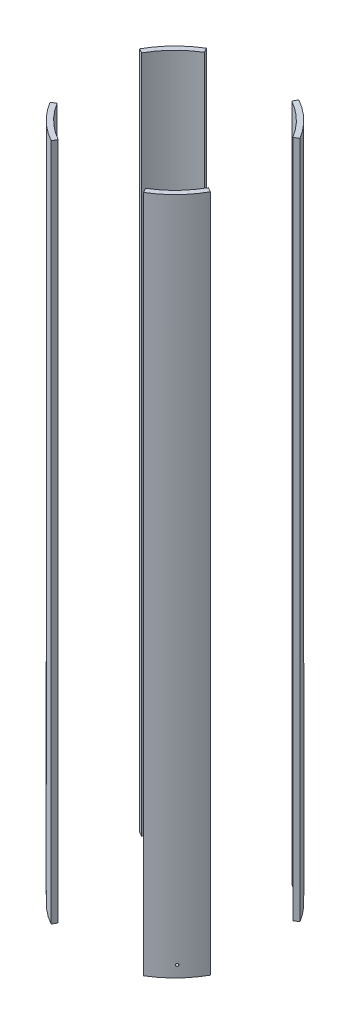
SolidWorks part; units mm, degrees
material "6061-T6 (SS)"
ref_plane "Front Plane" through (0, 0, 0) normal (0, 0, 1) x (1, 0, 0)
ref_plane "Top Plane" through (0, 0, 0) normal (0, 1, 0) x (1, 0, 0)
ref_plane "Right Plane" through (0, 0, 0) normal (1, 0, 0) x (0, 0, -1)
sketch "Sketch2" plane through (0, 0, 0) normal (0, 1, 0) x (1, 0, 0)
  circle A0 centre (0, 0) radius 88.9
  circle A1 centre (0, 0) radius 83.82
  dimension "D1" = 177.8
  dimension "D2" = 167.64
extrude "Boss-Extrude1" add sketch "Sketch2" along normal mid plane 662.3682
sketch "Sketch3" plane through (0, 0, 0) normal (0, 1, 0) x (1, 0, 0)
  line L0 (0, 0) -> (169.6618, 101.6776)
  line L1 (-58.1167, 96.9749) -> (0, 0)
  line L2 (0, 0) -> (53.9, 96.9749)
  line L3 (53.9, 96.9749) -> (-58.1167, 96.9749)
  line L4 (0, 0) -> (70.9917, -118.4586)
  line L5 (70.9917, -118.4586) -> (-65.8409, -118.4586)
  line L6 (-65.8409, -118.4586) -> (0, 0)
  line L7 (169.6618, 101.6776) -> (169.6618, -94.3004)
  line L8 (169.6618, -94.3004) -> (0, 0)
  line L9 (0, 0) -> (-123.7413, 68.7771)
  line L10 (-123.7413, 68.7771) -> (-123.7413, -74.1577)
  line L11 (-123.7413, -74.1577) -> (0, 0)
  dimension "D1" = 60
  dimension "D2" = 60
  dimension "D3" = 60
  dimension "D4" = 60
  dimension "D5" = 30
  dimension "D6" = 30
extrude "Cut-Extrude1" cut sketch "Sketch3" against normal through all both and the other way through all contours L8 L7 L0 | L2 L3 L1 | L10 L11 L9 | L6 L5 L4
ref_plane "Bolt reference plane" through (-56.3092, 0, 58.1758) normal (0.6955, 0, -0.7185) x (-0.7185, 0, -0.6955)
sketch "Bolt hole centerline" plane through (0, -331.1841, 0) normal (0, -1, 0) x (1, 0, 0)
  line L0 (-71.8974, 43.0878) -> (-40.7211, 73.2638) construction
  line L1 (-56.3092, 58.1758) -> (0, 0) construction
  point P7 (0, 0)
sketch "Sketch5" plane through (-56.3092, 0, 58.1758) normal (0.6955, 0, -0.7185) x (-0.7185, 0, -0.6955)
  line L0 (-23.009, -331.1841) -> (23.009, -331.1841) construction
  circle A1 centre (0, -320.0716) radius 1.27
  point P0 (0, 0)
  dimension "D1" = 2.54
  dimension "D4" = 11.1125
extrude "Bolt holes" cut sketch "Sketch5" against normal through all
pattern_circular "Bolt pattern" count 4 over 360 about axis through (0, 331.1841, 0) along (0, 1, 0) of "Bolt holes"
equation "\"D1@Boss-Extrude1\"=3*12"
